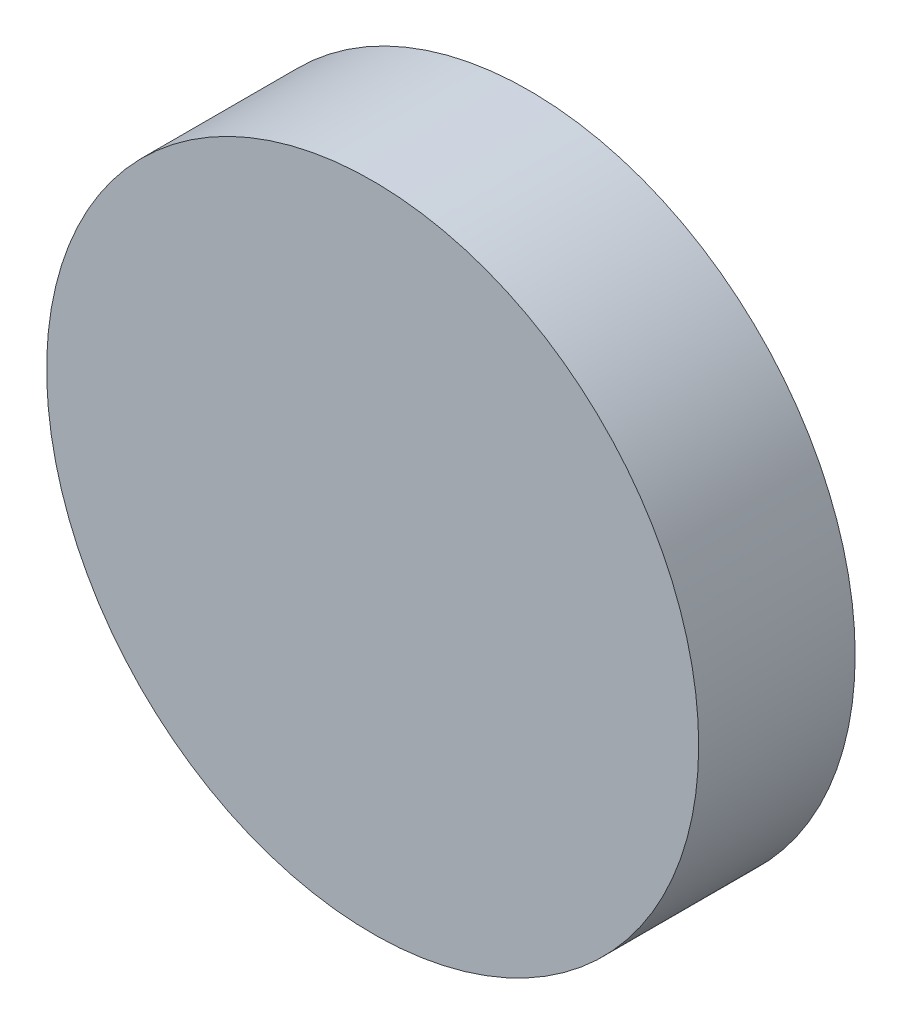
SolidWorks part; units mm, degrees
ref_plane "前视基准面" through (0, 0, 0) normal (0, 0, 1) x (1, 0, 0)
ref_plane "上视基准面" through (0, 0, 0) normal (0, 1, 0) x (1, 0, 0)
ref_plane "右视基准面" through (0, 0, 0) normal (1, 0, 0) x (0, 0, -1)
sketch "草图1" plane through (0, 0, 0) normal (0, 0, 1) x (1, 0, 0)
  circle A0 centre (0, 0) radius 6.25
  dimension "D1" = 12.5
extrude "凸台-拉伸1" add sketch "草图1" along normal blind 3 contours A0
